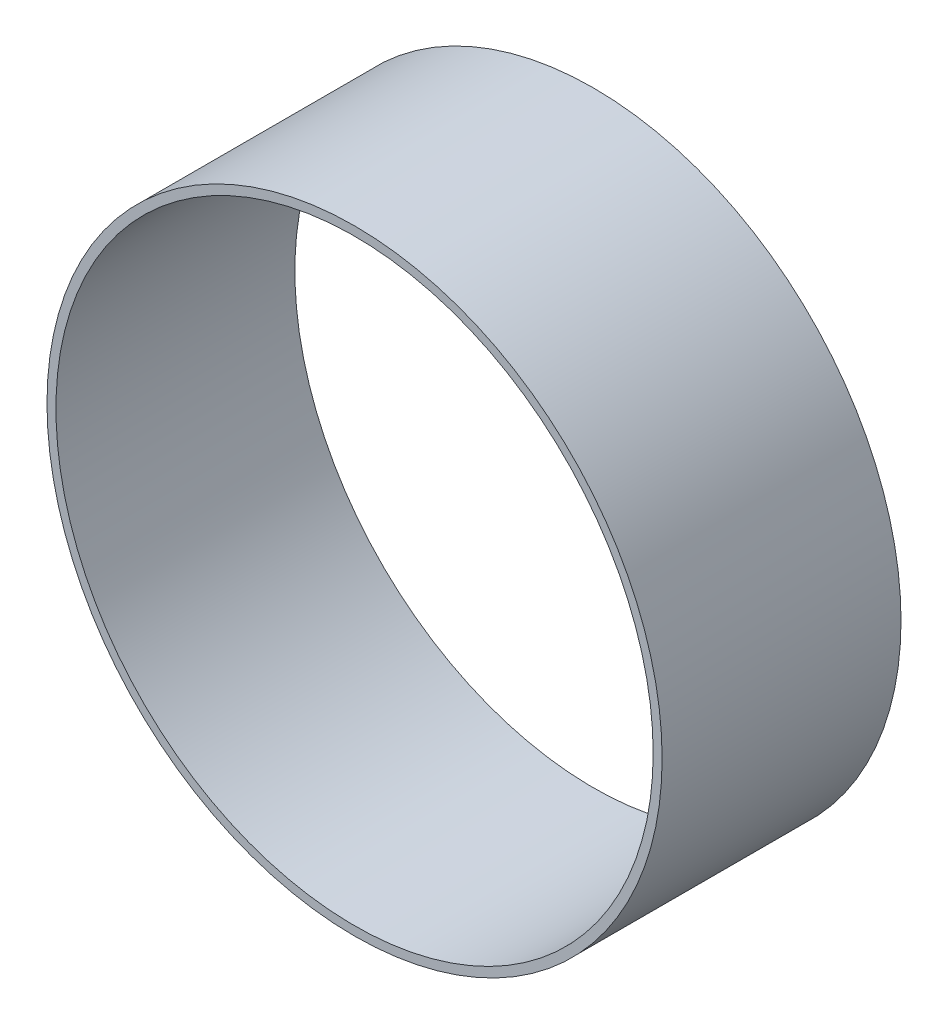
SolidWorks part; units mm, degrees
ref_plane "Front Plane" through (0, 0, 0) normal (0, 0, 1) x (1, 0, 0)
ref_plane "Top Plane" through (0, 0, 0) normal (0, 1, 0) x (1, 0, 0)
ref_plane "Right Plane" through (0, 0, 0) normal (1, 0, 0) x (0, 0, -1)
sketch "Sketch1" plane through (0, 0, 0) normal (0, 0, 1) x (1, 0, 0)
  circle A0 centre (0, 0) radius 65.405
  circle A1 centre (0, 0) radius 63.5
  dimension "D1" = 127
  dimension "D2" = 130.81
extrude "Boss-Extrude1" add sketch "Sketch1" along normal mid plane 50.8
equation "\"AIRFRAME_OD\"= 5.15in"
equation "\"AIRFRAME_ID\"= 5.00in"
equation "\"FLAT_T\"= 0.125in"
equation "\"NOSE_EXP_L\"= 27in"
equation "\"NOSE_SHOULDER_L\"= 5in"
equation "\"MAIN_L\"= 30in"
equation "\"RECO_COUP_L\"= 10in"
equation "\"RECO_SWITCH_L\"= 2in"
equation "\"DROGUE_L\"= 20in"
equation "\"ATS_FORE_COUP_L\"= 5.5in"
equation "\"ATS_AFT_COUP_L\"= 4.5in"
equation "\"LOWER_L\"= 30in"
equation "\"FIN_N\"= 4"
equation "\"CR_AFT_X\"= 0.5in"
equation "\"CR_FORE_X\"= 9.25in"
equation "\"D1@Sketch1\"=\"AIRFRAME_ID\""
equation "\"D2@Sketch1\"=\"AIRFRAME_OD\""
equation "\"D1@Boss-Extrude1\"=\"RECO_SWITCH_L\""
equation "\"FIN_ROOT\"= 8in"
equation "\"FIN_X\"= 0.75in"
equation "\"MOTOR_OD\"= 3.091in"
equation "\"MOTOR_ID\"= 3.00in"
equation "\"COUPLER_OD\"= 4.998in"
equation "\"COUPLER_ID\"= 4.88in"
equation "\"RECO_ROD_X\"= 3.5in"
equation "\"ATS_ROD_X\"= 3.75in"
equation "\"MOTOR_L\"= 14in"
equation "\"MOTOR_LOWER_X\"= 2in"
